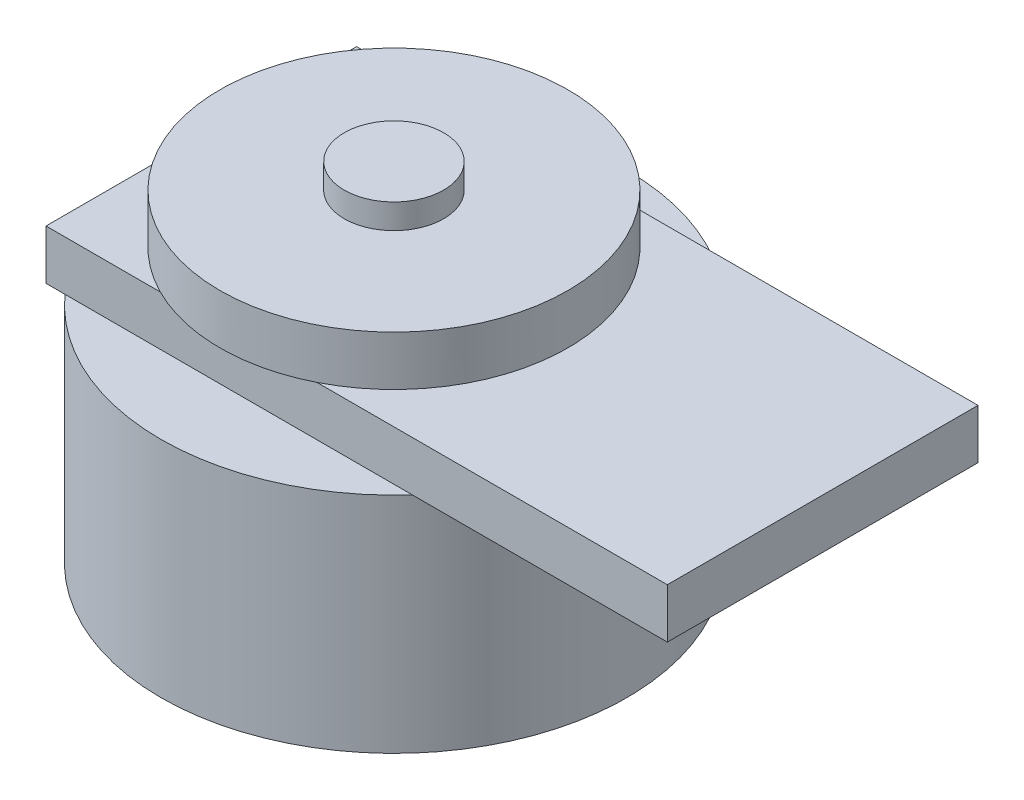
SolidWorks part; units mm, degrees
ref_plane "Front Plane" through (0, 0, 0) normal (0, 0, 1) x (1, 0, 0)
ref_plane "Top Plane" through (0, 0, 0) normal (0, 1, 0) x (1, 0, 0)
ref_plane "Right Plane" through (0, 0, 0) normal (1, 0, 0) x (0, 0, -1)
sketch "Sketch1" plane through (0, 0, 0) normal (0, 1, 0) x (1, 0, 0)
  line L6 (25, -12.5) -> (-25, -12.5)
  line L7 (25, -12.5) -> (25, 12.5)
  line L8 (25, 12.5) -> (-25, 12.5)
  line L9 (-25, -12.5) -> (-25, 12.5)
  line L10 (25, -12.5) -> (-25, 12.5) construction
  line L11 (25, 12.5) -> (-25, -12.5) construction
  point P0 (0, 0)
  point P1 (0, 0)
  dimension "D1" = 25
  dimension "D2" = 50
extrude "Boss-Extrude1" add sketch "Sketch1" along normal blind 4
sketch "Sketch2" plane through (0, 4, 0) normal (0, 1, 0) x (1, 0, 0)
  line L0 (-55, 0) -> (55, 0) construction
  line L1 (25, -12.5) -> (25, 12.5) construction
  circle A0 centre (-9.5, 0) radius 14
  dimension "D1" = 28
  dimension "D2" = 34.5
extrude "Boss-Extrude2" add sketch "Sketch2" along normal blind 4
sketch "Sketch3" plane through (0, 8, 0) normal (0, 1, 0) x (1, 0, 0)
  circle A0 centre (-9.5, 0) radius 4
  dimension "D1" = 8
extrude "Boss-Extrude3" add sketch "Sketch3" along normal blind 2
sketch "Sketch4" plane through (0, 0, 0) normal (0, -1, 0) x (1, 0, 0)
  circle A0 centre (-9.5, 0) radius 18.75
  dimension "D1" = 37.5
extrude "Boss-Extrude4" add sketch "Sketch4" along normal blind 18
